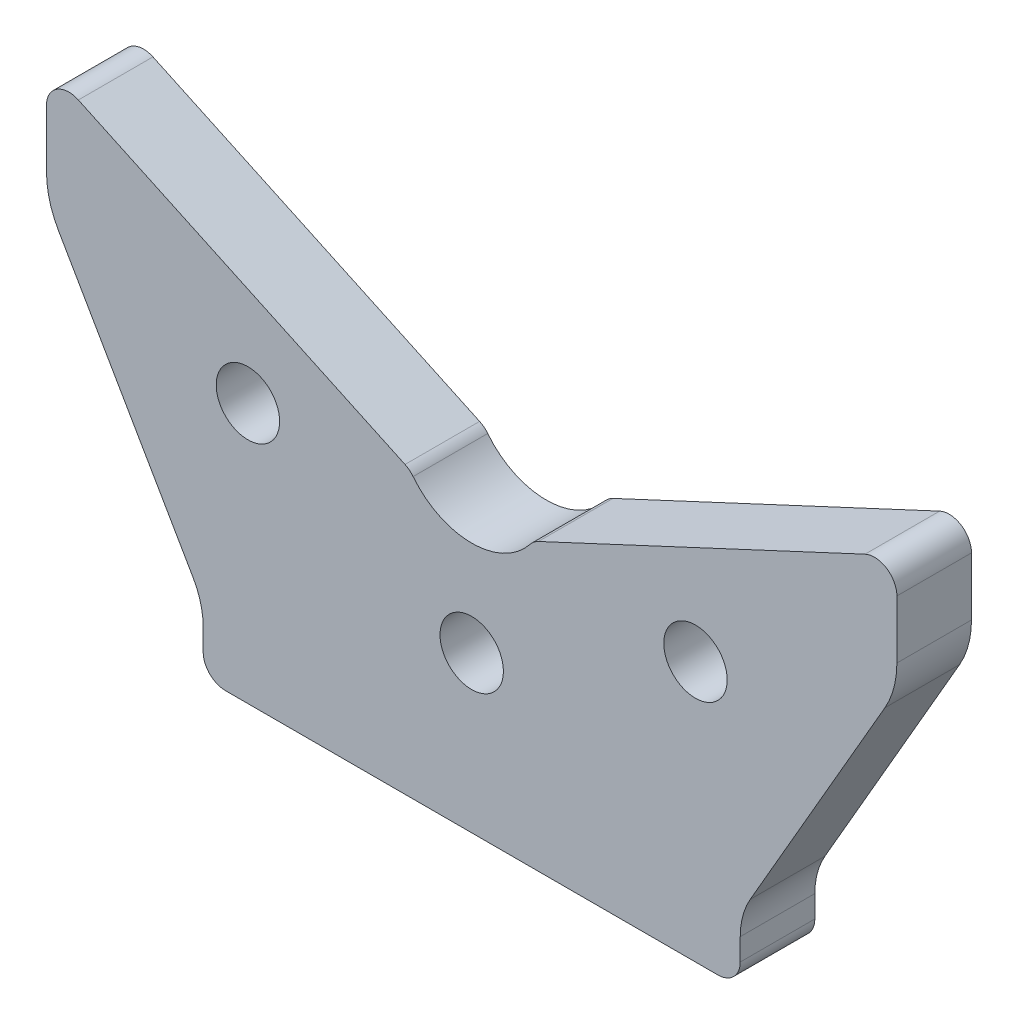
SolidWorks part; units mm, degrees
ref_plane "Front" through (0, 0, 0) normal (0, 0, 1) x (1, 0, 0)
ref_plane "Top" through (0, 0, 0) normal (0, 1, 0) x (1, 0, 0)
ref_plane "Right" through (0, 0, 0) normal (1, 0, 0) x (0, 0, -1)
sketch "Sketch1" plane through (0, 0, 0) normal (0, 0, 1) x (1, 0, 0)
  line L0 (-37.3397, 10.9474) -> (-55.3923, 42.2154)
  line L1 (37.3397, 10.9474) -> (55.3923, 42.2154)
  line L2 (0, 0) -> (33, 0)
  line L3 (0, 0) -> (-33, 0)
  line L4 (52.7321, 58.7189) -> (8.9396, 38.2981)
  line L5 (0, 0) -> (0, 34.1295) construction
  line L6 (-57, 48.2154) -> (-57, 56)
  line L7 (-52.7321, 58.7189) -> (-8.9396, 38.2981)
  line L8 (36, 3) -> (36, 5.9474)
  line L10 (57, 48.2154) -> (57, 56)
  line L11 (-36, 3) -> (-36, 5.9474)
  arc A0 (-36, 5.9474) -> (-37.3397, 10.9474) centre (-46, 5.9474) ccw
  arc A1 (36, 5.9474) -> (37.3397, 10.9474) centre (46, 5.9474) cw
  arc A3 (52.7321, 58.7189) -> (57, 56) centre (54, 56) cw
  arc A4 (-57, 56) -> (-52.7321, 58.7189) centre (-54, 56) cw
  arc A5 (55.3923, 42.2154) -> (57, 48.2154) centre (45, 48.2154) ccw
  arc A7 (36, 3) -> (33, 0) centre (33, 3) cw
  arc A8 (-36, 3) -> (-33, 0) centre (-33, 3) ccw
  arc A9 (-55.3923, 42.2154) -> (-57, 48.2154) centre (-45, 48.2154) cw
  arc A10 (-7.8519, 37.437) -> (7.8519, 37.437) centre (0, 43.6295) ccw
  arc A11 (-7.8519, 37.437) -> (-8.9396, 38.2981) centre (-10.2075, 35.5792) ccw
  arc A12 (7.8519, 37.437) -> (8.9396, 38.2981) centre (10.2075, 35.5792) cw
  point P19 (57, 60.7091)
  point P23 (-57, 60.7091)
  point P26 (57, 0)
  point P32 (57, 45)
  point P43 (0, 34.1295)
  dimension "D5" = 14
  dimension "D6" = 3
  dimension "D7" = 43.9282
  dimension "D8" = 34.1295
  dimension "D13" = 12
  dimension "D15" = 10
  dimension "D16" = 3
  dimension "D2" = 3
  dimension "D17" = 10
  dimension "D3" = 65
  dimension "D4" = 25
  dimension "D9" = 114
  dimension "D10" = 59
  dimension "D11" = 30
  dimension "D12" = 72
  dimension "D14" = 9.5
extrude "Extrude1" add sketch "Sketch1" along normal blind 10
hole_wizard "M10 gevindhuller" positions "Sketch5" profile "Sketch4" legacy
sketch "Sketch5" plane through (0, 0, 10) normal (0, 0, 1) x (1, 0, 0)
  line L0 (0, 0) -> (0, 43.6295) construction
  line L1 (52.7321, 58.7189) -> (8.9396, 38.2981) construction
  line L2 (30, 34.8782) -> (52.6835, 45.4557) construction
  line L3 (30, 34.8782) -> (0, 20.8782) construction
  point P6 (-30, 34.8782)
  point P11 (30, 34.8782)
  point P22 (0, 20.8782)
  dimension "D1" = 60
  dimension "D2" = 12
  dimension "D3" = 14
sketch "Sketch4" plane through (-30, 34.8782, 10) normal (1, 0, 0) x (0, -1, 0)
  line L0 (0, 0) -> (0, 24.5537)
  line L1 (0, 24.5537) -> (4.25, 22)
  line L2 (4.25, 22) -> (4.25, 0)
  line L4 (4.25, 0) -> (0, 0)
  line L6 (0, 24.5537) -> (-4.25, 22) construction
  line L7 (0, -4.2442) -> (0, 117.3081) construction
  dimension "Diameter" = 8.5
  dimension "Depth" = 22
  dimension "Drill Angle" = 118
cosmetic thread "Cosmetic Thread2" parameters "D1"=17, "D2"=10
cosmetic thread "Cosmetic Thread3" parameters "D1"=17, "D2"=10
cosmetic thread "Cosmetic Thread4" parameters "D2"=10
